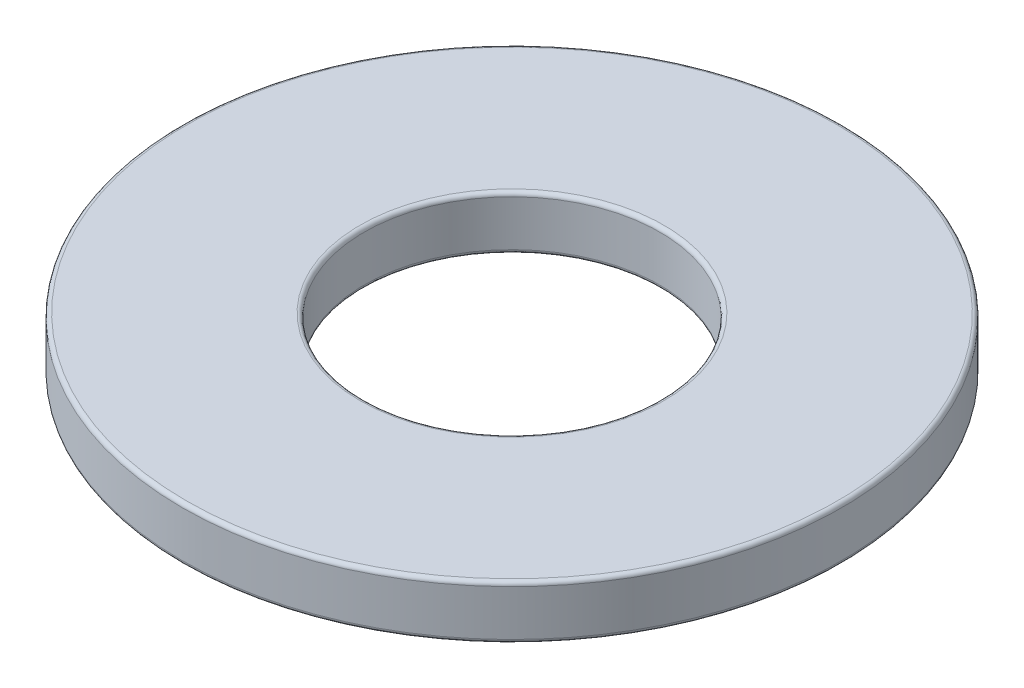
SolidWorks part; units mm, degrees
ref_plane "Front Plane" through (0, 0, 0) normal (0, 0, 1) x (1, 0, 0)
ref_plane "Top Plane" through (0, 0, 0) normal (0, 1, 0) x (1, 0, 0)
ref_plane "Right Plane" through (0, 0, 0) normal (1, 0, 0) x (0, 0, -1)
sketch "Sketch1" plane through (0, 0, 0) normal (0, 1, 0) x (1, 0, 0)
  circle A0 centre (0, 0) radius 2.2
  circle A1 centre (0, 0) radius 4.9
extrude "Boss-Extrude1" add sketch "Sketch1" along normal blind 0.8
fillet "Fillet1" radius 0.06 4 edges at (0, 0.8, 2.2) (0, 0, 4.9) (0, 0, 2.2) (0, 0.8, 4.9)
